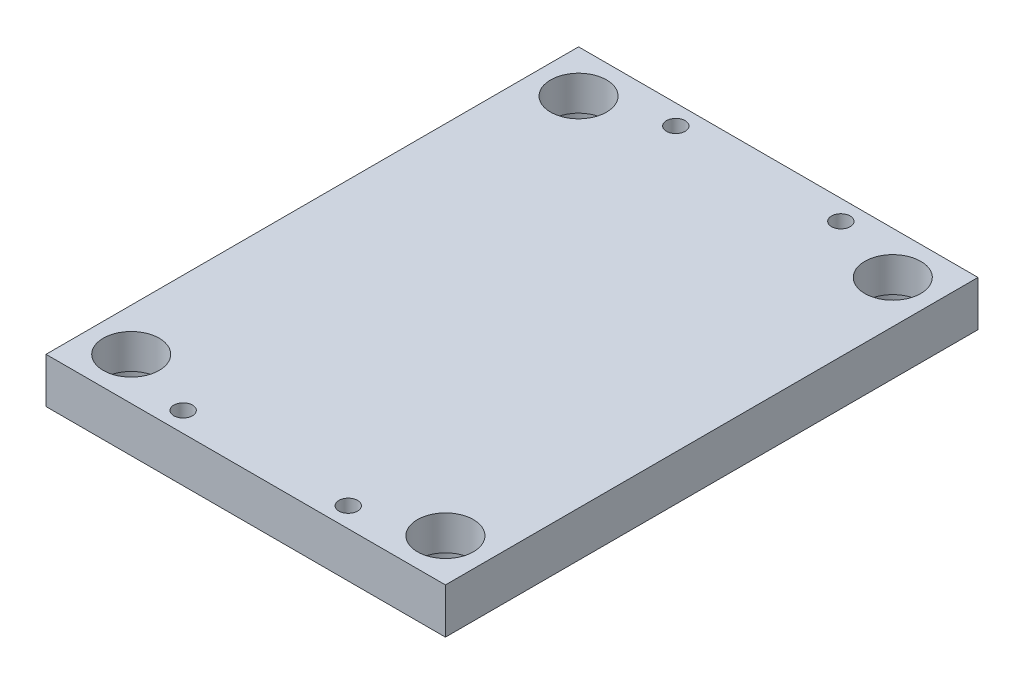
SolidWorks part; units mm, degrees
material "AISI 1020"
ref_plane "Plano frontal" through (0, 0, 0) normal (0, 0, 1) x (1, 0, 0)
ref_plane "Plano superior" through (0, 0, 0) normal (0, 1, 0) x (1, 0, 0)
ref_plane "Plano direito" through (0, 0, 0) normal (1, 0, 0) x (0, 0, -1)
sketch "Esboço1" plane through (0, 0, 0) normal (0, 1, 0) x (1, 0, 0)
  line L0 (150, 200) -> (-150, -200) construction
  line L1 (-150, 200) -> (150, 200)
  line L2 (-150, 200) -> (-150, -200)
  line L3 (-150, -200) -> (150, -200)
  line L4 (150, 200) -> (150, -200)
  dimension "D1" = 300
  dimension "D2" = 400
extrude "Extrusão1" add sketch "Esboço1" along normal blind 34
hole_wizard "Furo roscado de M161" positions "Esboço3" profile "Esboço2" tap size "M16" standard "ISO"
sketch "Esboço3" plane through (0, 0, 0) normal (0, -1, 0) x (1, 0, 0)
  point P0 (-118, 119)
  point P1 (118, 119)
  point P3 (-118, -119)
  point P5 (118, -119)
  dimension "D1" = 118
  dimension "D2" = 119
  dimension "D3" = 236
  dimension "D4" = 238
sketch "Esboço2" plane through (-118, 0, 119) normal (1, 0, 0) x (0, 0, -1)
  line L0 (0, 0) -> (0, 32.206)
  line L1 (0, 32.206) -> (7, 28)
  line L2 (7, 28) -> (7, 0)
  line L5 (7, 0) -> (0, 0)
  line L10 (0, 32.206) -> (-7, 28) construction
  line L11 (0, -6.35) -> (0, 107.95) construction
  dimension "Tap Drill Dia." = 14
  dimension "Tap Drill Depth" = 28
  dimension "Drill Angle" = 118
cosmetic thread "Rosca de furo1" parameters "D1"=18, "D2"=16
cosmetic thread "Rosca de furo2" parameters "D1"=18, "D2"=16
cosmetic thread "Rosca de furo3" parameters "D1"=18, "D2"=16
cosmetic thread "Rosca de furo4" parameters "D1"=18, "D2"=16
hole_wizard "Furo1" positions "Esboço5" profile "Esboço4" legacy end condition through all
sketch "Esboço5" plane through (0, 0, 0) normal (0, -1, 0) x (1, 0, 0)
  point P0 (118, 168)
  point P1 (118, -168)
  point P3 (-118, -168)
  point P5 (-118, 168)
  dimension "D1" = 236
  dimension "D2" = 118
  dimension "D3" = 336
  dimension "D4" = 168
sketch "Esboço4" plane through (118, 0, 168) normal (1, 0, 0) x (0, 0, -1)
  line L0 (0, 0) -> (0, 34)
  line L1 (0, 34) -> (21, 34)
  line L2 (21, 34) -> (21, 8)
  line L3 (21, 8) -> (24, 8)
  line L4 (24, 8) -> (24, 0)
  line L5 (24, 0) -> (0, 0)
  line L6 (0, 110) -> (0, -10) construction
  dimension "Diameter" = 42
  dimension "Depth" = 34
  dimension "C-Bore Diameter" = 48
  dimension "C-Bore Depth" = 8
hole_wizard "Furo2" positions "Esboço7" profile "Esboço6" legacy
sketch "Esboço7" plane through (0, 0, 0) normal (0, -1, 0) x (1, 0, 0)
  point P0 (-62, 185)
  point P1 (-62, -185)
  point P3 (62, 185)
  point P5 (62, -185)
  dimension "D1" = 124
  dimension "D2" = 370
  dimension "D3" = 62
  dimension "D4" = 185
sketch "Esboço6" plane through (-62, 0, 185) normal (1, 0, 0) x (0, 0, -1)
  line L0 (0, 0) -> (0, 100)
  line L1 (0, 100) -> (7, 100)
  line L2 (7, 100) -> (7, 0)
  line L3 (7, 0) -> (0, 0)
  line L4 (0, 110) -> (0, -10) construction
  dimension "Diameter" = 14
  dimension "Depth" = 100
